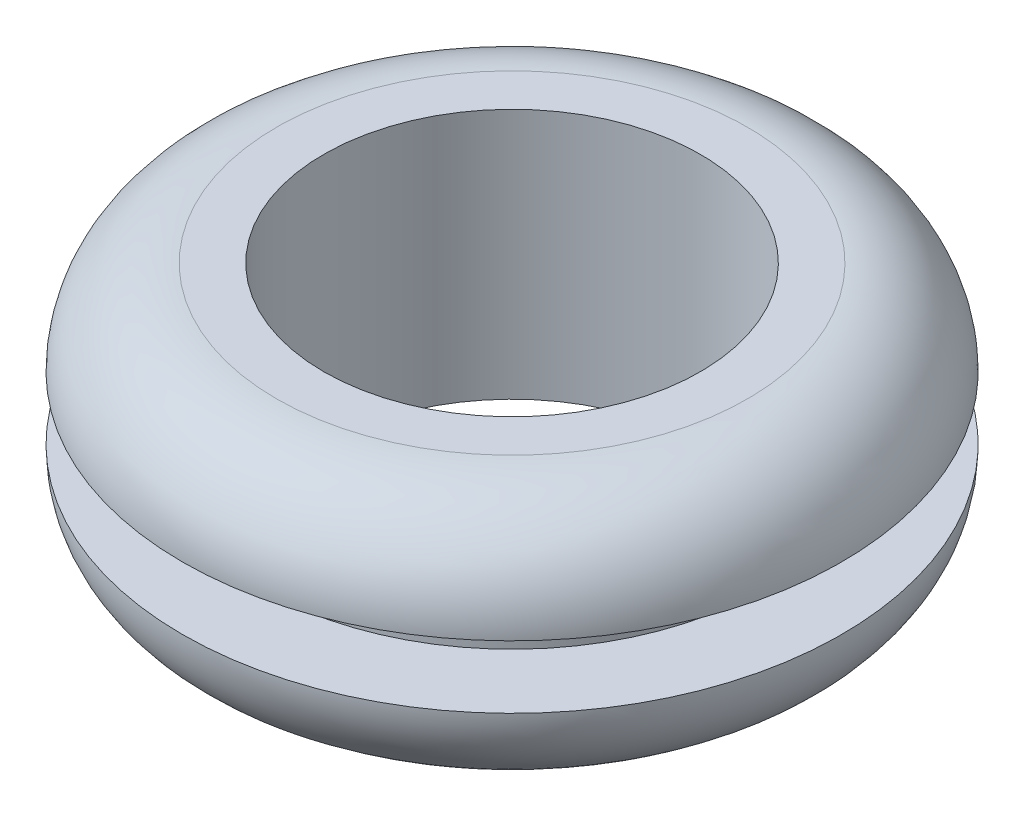
SolidWorks part; units mm, degrees
ref_plane "Front" through (0, 0, 0) normal (0, 0, 1) x (1, 0, 0)
ref_plane "Top" through (0, 0, 0) normal (0, 1, 0) x (1, 0, 0)
ref_plane "Right" through (0, 0, 0) normal (1, 0, 0) x (0, 0, -1)
sketch "Sketch1" plane through (0, 0, 0) normal (0, 0, 1) x (1, 0, 0)
  line L0 (-4.7625, 0) -> (4.7625, 0) construction
  line L1 (-6.35, 0) -> (6.35, 0) construction
  line L2 (0, 3.175) -> (0, -3.175) construction
  line L3 (8.3344, 3.175) -> (-8.3344, 3.175) construction
  line L4 (6.35, 0.7937) -> (6.35, -0.7937) construction
  dimension "ID" = 9.525
  dimension "for hole dia" = 12.7
  dimension "oall ht" = 6.35
  dimension "flange dia" = 16.6687
  dimension "material thick" = 1.5875
sketch "Sketch2" plane through (0, 0, 0) normal (0, 0, 1) x (1, 0, 0)
  line L0 (6.35, 0.7937) -> (8.3344, 0.7938)
  line L1 (8.3344, 3.175) -> (8.3344, -3.175) construction
  line L2 (8.3344, 3.175) -> (-8.3344, 3.175) construction
  line L3 (4.7625, 3.175) -> (5.9531, 3.175)
  line L4 (6.35, 0.7937) -> (6.35, -0.7937)
  line L5 (4.7625, 3.175) -> (4.7625, -3.175)
  line L6 (4.7625, -3.175) -> (5.9531, -3.175)
  line L7 (8.3344, -0.7937) -> (6.35, -0.7937)
  arc A0 (5.9531, 3.175) -> (8.3344, 0.7938) centre (5.9531, 0.7937) cw
  arc A1 (5.9531, -3.175) -> (8.3344, -0.7937) centre (5.9531, -0.7938) ccw
revolve "Revolve1" add sketch "Sketch2" angle 360 about L2
